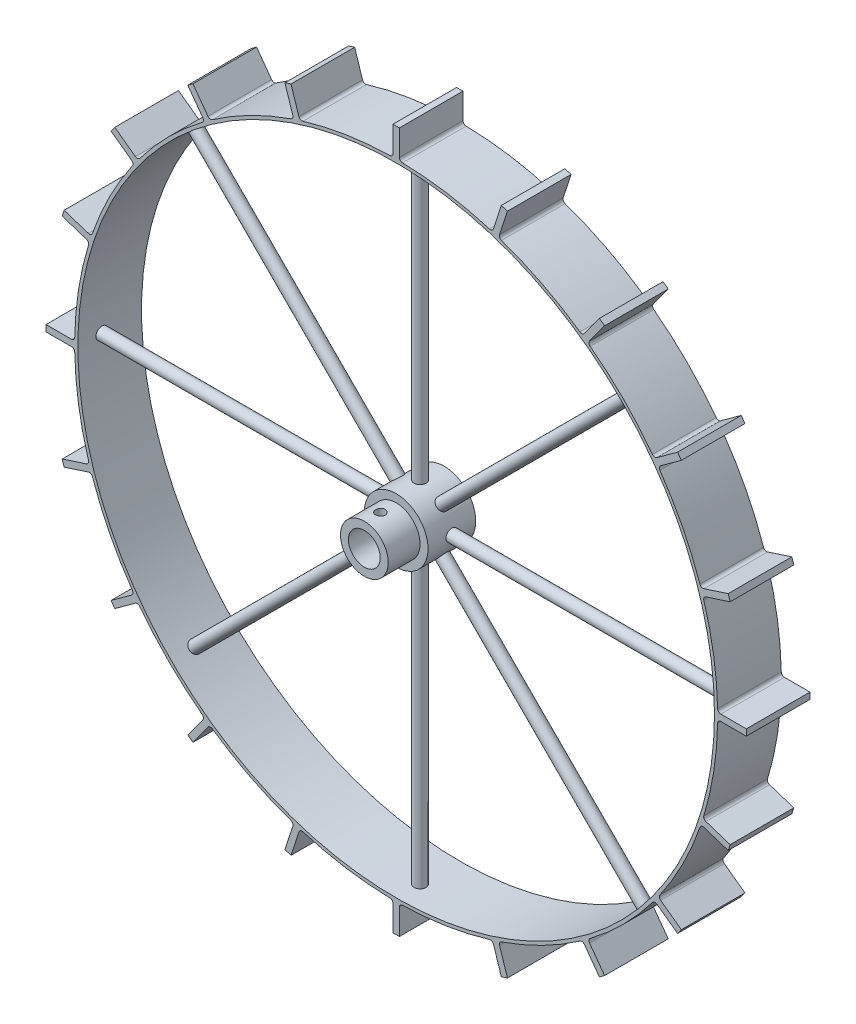
SolidWorks part; units mm, degrees
ref_plane "Front Plane" through (0, 0, 0) normal (0, 0, 1) x (1, 0, 0)
ref_plane "Top Plane" through (0, 0, 0) normal (0, 1, 0) x (1, 0, 0)
ref_plane "Right Plane" through (0, 0, 0) normal (1, 0, 0) x (0, 0, -1)
sketch "Sketch1" plane through (0, 0, 0) normal (0, 0, 1) x (1, 0, 0)
  circle A0 centre (0, 0) radius 25.4
  dimension "D1" = 50.8
extrude "Boss-Extrude1" add sketch "Sketch1" against normal blind 38.1
sketch "Sketch2" plane through (0, 0, 0) normal (0, 0, 1) x (1, 0, 0)
  circle A0 centre (0, 0) radius 12.7
  dimension "D1" = 25.4
extrude "Cut-Extrude1" cut sketch "Sketch2" against normal blind 50.8
sketch "Sketch3" plane through (0, 0, 0) normal (0, 0, 1) x (1, 0, 0)
  line L0 (0, 0) -> (0, 12.7) construction
  line L2 (-3, 10.1385) -> (3, 10.1385)
  line L3 (-3, 10.1385) -> (-3, 15.2615)
  line L4 (-3, 15.2615) -> (3, 15.2615)
  line L5 (3, 10.1385) -> (3, 15.2615)
  line L6 (-3, 10.1385) -> (3, 15.2615) construction
  line L7 (-3, 15.2615) -> (3, 10.1385) construction
  circle A0 centre (0, 0) radius 12.7 construction
  dimension "D1" = 6
extrude "Cut-Extrude2" [suppressed] cut sketch "Sketch3" against normal through all
ref_plane "Plane1" through (0, 0, -19.05) normal (0, 0, 1) x (1, 0, 0)
sketch "Sketch8" plane through (0, 0, -19.05) normal (0, 0, 1) x (1, 0, 0)
  line L0 (0, 25.4) -> (0, 254)
  circle A0 centre (0, 0) radius 25.4 construction
  dimension "D1" = 228.6
sketch "Sketch9" plane through (0, 0, -19.05) normal (0, 0, 1) x (1, 0, 0)
  line L0 (0, -25.4) -> (0, -254)
  line L1 (25.4, 0) -> (254, 0)
  line L2 (-25.4, 0) -> (-254, 0)
  line L3 (0, 0) -> (179.6051, 179.6051)
  line L4 (0, 0) -> (-179.6051, -179.6051)
  line L5 (0, 0) -> (-179.6051, 179.6051)
  line L6 (0, 0) -> (179.6051, -179.6051)
  circle A0 centre (0, 0) radius 25.4 construction
  dimension "D1" = 45
  dimension "D2" = 45
  dimension "D3" = 45
  dimension "D4" = 45
  dimension "D5" = 254
  dimension "D6" = 228.6
  dimension "D7" = 228.6
  dimension "D8" = 254
  dimension "D9" = 254
  dimension "D10" = 228.6
  dimension "D11" = 254
other "Al round tubing AL RND TUBE 0.375 OD X 0.035 WALL(1)"
ref_plane "Plane2" through (0, 25.4, -19.05) normal (0, 1, 0) x (-1, 0, 0)
sketch "Sketch18" plane through (0, 25.4, -19.05) normal (0, 1, 0) x (-1, 0, 0)
  circle A0 centre (0, 0) radius 3.8735
  circle A1 centre (0, 0) radius 4.7625
  point P3 (0, 0)
  dimension "In_dia" = 7.747
  dimension "Out_dia" = 9.525
sketch "Sketch12" plane through (0, 0, 0) normal (0, 0, 1) x (1, 0, 0)
  circle A0 centre (0, 0) radius 12.7
extrude "Cut-Extrude5" cut sketch "Sketch12" against normal mid plane 254
sketch "Sketch19" plane through (0, 0, 0) normal (0, 0, 1) x (1, 0, 0)
  circle A0 centre (0, 0) radius 254
  circle A1 centre (0, 0) radius 256.54
  dimension "D1" = 508
  dimension "D2" = 513.08
extrude "Boss-Extrude4" add sketch "Sketch19" against normal blind 50.8 separate body
sketch "Sketch20" plane through (0, 0, 0) normal (0, 0, 1) x (1, 0, 0)
  circle A0 centre (0, 0) radius 19.05
  circle A1 centre (0, 0) radius 12.7
  dimension "D1" = 38.1
extrude "Boss-Extrude5" add sketch "Sketch20" along normal blind 25.4 separate body
sketch "Sketch21" plane through (0, 0, 0) normal (0, 1, 0) x (1, 0, 0)
  circle A0 centre (0, -12.7) radius 3.81
  dimension "D1" = 7.62
extrude "Cut-Extrude7" cut sketch "Sketch21" along normal blind 19.05
ref_plane "Plane3" through (0, 279.4, 0) normal (0, 1, 0) x (1, 0, 0)
sketch "Sketch22" [suppressed] plane through (0, 256.54, 0) normal (0, 1, 0) x (1, 0, 0)
  line L0 (0, 50.8) -> (0, 0)
  line L1 (256.54, 50.8) -> (-256.54, 50.8) construction
sketch "Sketch111" plane through (0, 279.4, 0) normal (0, 1, 0) x (1, 0, 0)
  line L0 (256.54, 50.8) -> (-256.54, 50.8) construction
  line L1 (-2.5721, 50.8) -> (2.54, 50.8)
  line L2 (-2.5721, 50.8) -> (-2.5721, 0)
  line L3 (-2.5721, 0) -> (2.54, 0)
  line L4 (2.54, 50.8) -> (2.54, 0)
  line L5 (0, 50.8) -> (0, 0) construction
  line L7 (2.54, 50.8) -> (15.24, 50.8)
  line L8 (2.54, 50.8) -> (2.54, 0)
  line L9 (2.54, 0) -> (15.24, 0)
  line L10 (15.24, 50.8) -> (15.24, 0)
  dimension "D1" = 50.8
  dimension "D2" = 2.5721
  dimension "D3" = 2.54
  dimension "D4" = 12.7
extrude "Boss-Extrude8" add sketch "Sketch111" against normal up to surface (22.8729 mm away) contours L4 L3 L2 L1
fillet "Fillet1" radius 2.54 2 edges at (-2.5721, 256.5271, -25.4) (2.54, 256.5274, -25.4)
pattern_circular "CirPattern6" count 20 over 360 about axis through (0, 0, 0) along (0, 0, 1) of "Fillet1", "Boss-Extrude8"
